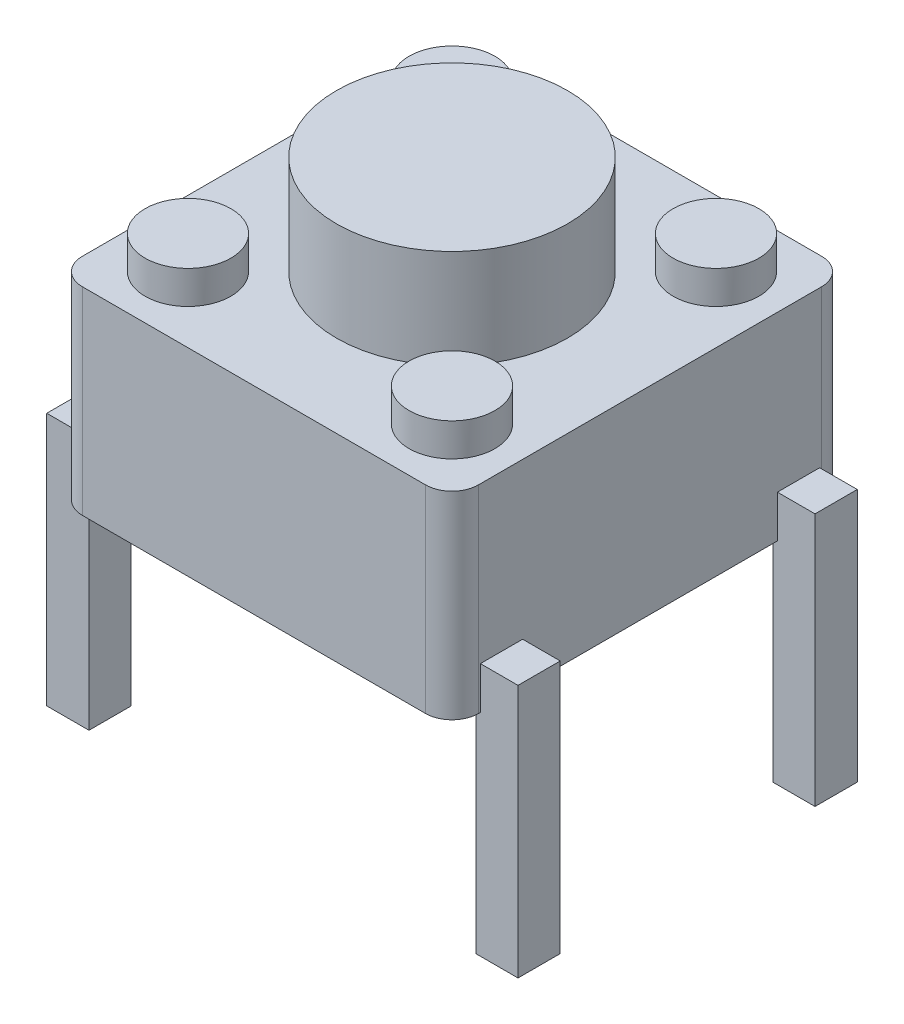
SolidWorks part; units mm, degrees
ref_plane "Front Plane" through (0, 0, 0) normal (0, 0, 1) x (1, 0, 0)
ref_plane "Top Plane" through (0, 0, 0) normal (0, 1, 0) x (1, 0, 0)
ref_plane "Right Plane" through (0, 0, 0) normal (1, 0, 0) x (0, 0, -1)
sketch "Sketch1" plane through (0, 0, 0) normal (0, 1, 0) x (1, 0, 0)
  line L1 (-3, -3) -> (3, -3)
  line L2 (-3, -3) -> (-3, 3)
  line L3 (-3, 3) -> (3, 3)
  line L4 (3, -3) -> (3, 3)
  line L5 (-3, -3) -> (3, 3) construction
  line L6 (-3, 3) -> (3, -3) construction
  point P0 (0, 0)
  dimension "D1" = 6
extrude "Boss-Extrude1" add sketch "Sketch1" along normal blind 3
sketch "Sketch2" plane through (0, 3, 0) normal (0, 1, 0) x (1, 0, 0)
  circle A0 centre (0, 0) radius 1.75
  dimension "D1" = 3.5
extrude "Boss-Extrude2" add sketch "Sketch2" along normal blind 1.5
sketch "Sketch3" plane through (0, 3, 0) normal (0, 1, 0) x (1, 0, 0)
  line L1 (-2, -2) -> (2, -2) construction
  line L2 (-2, -2) -> (-2, 2) construction
  line L3 (-2, 2) -> (2, 2) construction
  line L4 (2, -2) -> (2, 2) construction
  line L5 (-2, -2) -> (2, 2) construction
  line L6 (-2, 2) -> (2, -2) construction
  circle A0 centre (-2, 2) radius 0.65
  circle A1 centre (-2, -2) radius 0.65
  circle A2 centre (2, -2) radius 0.65
  circle A3 centre (2, 2) radius 0.65
  point P0 (0, 0)
  dimension "D1" = 1.3
  dimension "D2" = 4
extrude "Boss-Extrude3" add sketch "Sketch3" along normal blind 0.5
sketch "Sketch4" plane through (0, 0, 0) normal (0, -1, 0) x (1, 0, 0)
  line L1 (-3.25, -2.25) -> (3.25, -2.25) construction
  line L2 (-3.25, -2.25) -> (-3.25, 2.25) construction
  line L3 (-3.25, 2.25) -> (3.25, 2.25) construction
  line L4 (3.25, -2.25) -> (3.25, 2.25) construction
  line L5 (-3.25, -2.25) -> (3.25, 2.25) construction
  line L6 (-3.25, 2.25) -> (3.25, -2.25) construction
  line L7 (-2.93, 1.93) -> (-3.57, 1.93)
  line L8 (-2.93, 1.93) -> (-2.93, 2.57)
  line L9 (-2.93, 2.57) -> (-3.57, 2.57)
  line L10 (-3.57, 1.93) -> (-3.57, 2.57)
  line L11 (-2.93, 1.93) -> (-3.57, 2.57) construction
  line L12 (-2.93, 2.57) -> (-3.57, 1.93) construction
  line L13 (2.93, 1.93) -> (3.57, 1.93)
  line L14 (2.93, 1.93) -> (2.93, 2.57)
  line L15 (2.93, 2.57) -> (3.57, 2.57)
  line L16 (3.57, 1.93) -> (3.57, 2.57)
  line L17 (2.93, 1.93) -> (3.57, 2.57) construction
  line L18 (2.93, 2.57) -> (3.57, 1.93) construction
  line L19 (2.93, -2.57) -> (3.57, -2.57)
  line L20 (2.93, -2.57) -> (2.93, -1.93)
  line L21 (2.93, -1.93) -> (3.57, -1.93)
  line L22 (3.57, -2.57) -> (3.57, -1.93)
  line L23 (2.93, -2.57) -> (3.57, -1.93) construction
  line L24 (2.93, -1.93) -> (3.57, -2.57) construction
  line L25 (-2.93, -2.57) -> (-3.57, -2.57)
  line L26 (-2.93, -2.57) -> (-2.93, -1.93)
  line L27 (-2.93, -1.93) -> (-3.57, -1.93)
  line L28 (-3.57, -2.57) -> (-3.57, -1.93)
  line L29 (-2.93, -2.57) -> (-3.57, -1.93) construction
  line L30 (-2.93, -1.93) -> (-3.57, -2.57) construction
  point P0 (0, 0)
  dimension "D1" = 0.64
  dimension "D2" = 6.5
  dimension "D3" = 4.5
extrude "Boss-Extrude4" add sketch "Sketch4" along normal blind 3.2
fillet "Fillet1" radius 0.4 4 edges at (3, 1.5, -3) (3, 1.5, 3) (-3, 1.5, -3) (-3, 1.5, 3)
sketch "Sketch6" plane through (-3.57, 0, 0) normal (-1, 0, 0) x (0, 0, 1)
  line L1 (-2.57, 0) -> (-1.93, 0)
  line L2 (-2.57, 0) -> (-2.57, 0.64)
  line L3 (-2.57, 0.64) -> (-1.93, 0.64)
  line L4 (-1.93, 0) -> (-1.93, 0.64)
  line L5 (1.93, 0) -> (2.57, 0)
  line L6 (1.93, 0) -> (1.93, 0.64)
  line L7 (1.93, 0.64) -> (2.57, 0.64)
  line L8 (2.57, 0) -> (2.57, 0.64)
  dimension "D1" = 0.64
extrude "Boss-Extrude6" add sketch "Sketch6" against normal up to surface (7.14 mm away) up to face at (3.57, -1.6, 2.25)
